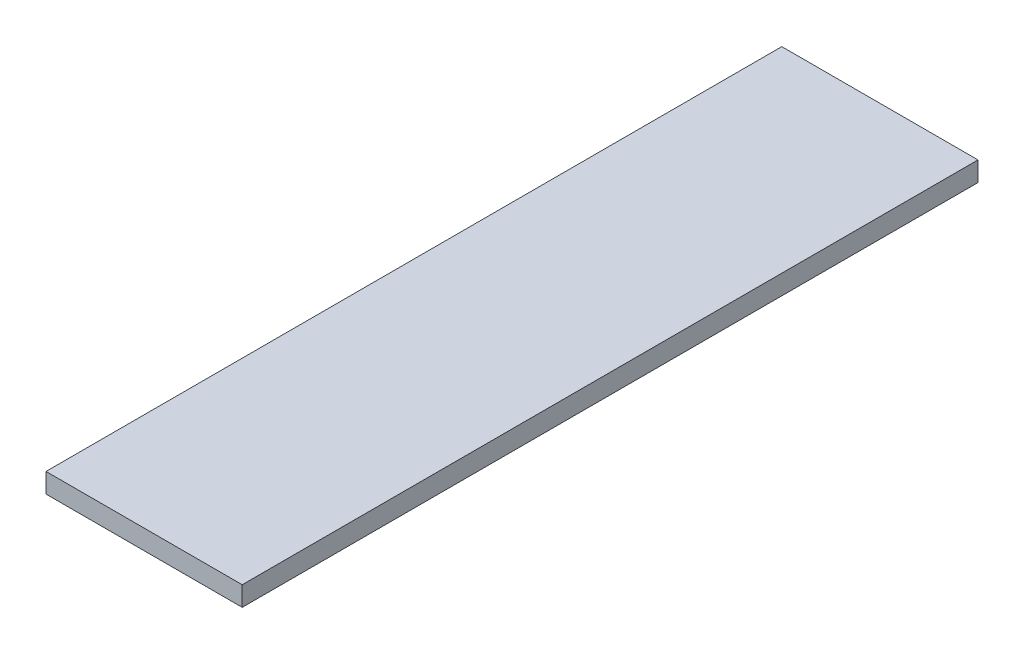
SolidWorks part; units mm, degrees
ref_plane "Plano frontal" through (0, 0, 0) normal (0, 0, 1) x (1, 0, 0)
ref_plane "Plano superior" through (0, 0, 0) normal (0, 1, 0) x (1, 0, 0)
ref_plane "Plano direito" through (0, 0, 0) normal (1, 0, 0) x (0, 0, -1)
sketch "Esboço1" plane through (0, 0, 0) normal (0, 0, 1) x (1, 0, 0)
  line L1 (-239.7981, 53.626) -> (-39.7981, 53.626)
  line L2 (-239.7981, 53.626) -> (-239.7981, 33.626)
  line L3 (-239.7981, 33.626) -> (-39.7981, 33.626)
  line L4 (-39.7981, 53.626) -> (-39.7981, 33.626)
  dimension "D1" = 200
  dimension "D2" = 20
extrude "Ressalto-extrusão1" add sketch "Esboço1" along normal blind 750
